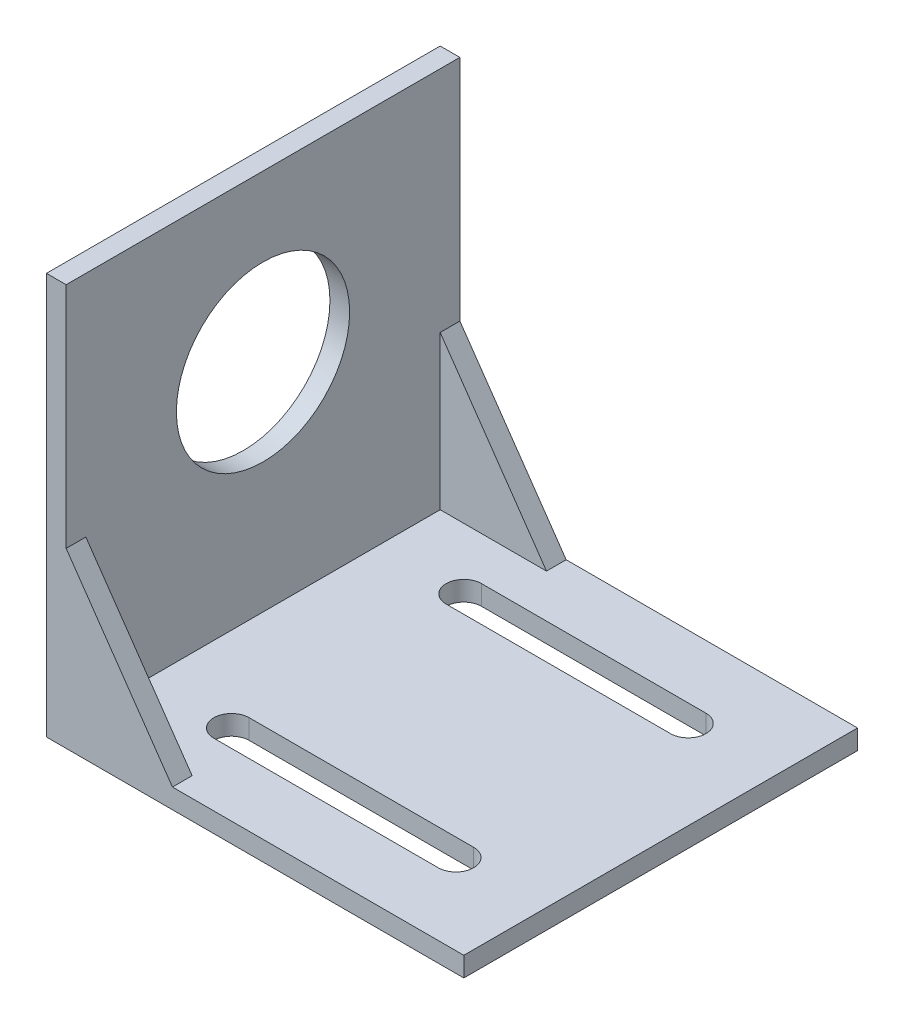
SolidWorks part; units mm, degrees
ref_plane "Front Plane" through (0, 0, 0) normal (0, 0, 1) x (1, 0, 0)
ref_plane "Top Plane" through (0, 0, 0) normal (0, 1, 0) x (1, 0, 0)
ref_plane "Right Plane" through (0, 0, 0) normal (1, 0, 0) x (0, 0, -1)
sketch "Sketch1" plane through (0, 0, 0) normal (0, 0, 1) x (1, 0, 0)
  line L0 (53, 0) -> (0, 0)
  line L1 (0, 0) -> (0, 51)
  line L2 (0, 51) -> (2.5, 51)
  line L3 (2.5, 51) -> (2.5, 2.5)
  line L4 (2.5, 2.5) -> (53, 2.5)
  line L5 (53, 2.5) -> (53, 0)
  dimension "D1" = 51
  dimension "D2" = 53
  dimension "D3" = 2.5
  dimension "D4" = 2.5
extrude "Boss-Extrude1" add sketch "Sketch1" along normal mid plane 50
sketch "Sketch5" plane through (0, 2.5, 0) normal (0, 1, 0) x (1, 0, 0)
  line L0 (13.25, 14.75) -> (41.75, 14.75) construction
  line L1 (13.25, 17) -> (41.75, 17)
  line L2 (13.25, 12.5) -> (41.75, 12.5)
  line L3 (13.25, -14.75) -> (41.75, -14.75) construction
  line L4 (13.25, -12.5) -> (41.75, -12.5)
  line L5 (13.25, -17) -> (41.75, -17)
  line L6 (53, -25) -> (53, 25) construction
  line L7 (0, 0) -> (53, 0) construction
  line L9 (0, -25) -> (0, 25) construction
  line L11 (53, 25) -> (2.5, 25) construction
  line L13 (53, -25) -> (2.5, -25) construction
  arc A0 (13.25, 17) -> (13.25, 12.5) centre (13.25, 14.75) ccw
  arc A1 (41.75, 12.5) -> (41.75, 17) centre (41.75, 14.75) ccw
  arc A2 (13.25, -12.5) -> (13.25, -17) centre (13.25, -14.75) ccw
  arc A3 (41.75, -17) -> (41.75, -12.5) centre (41.75, -14.75) ccw
  point P2 (27.5, 14.75)
  point P7 (27.5, -14.75)
  point P14 (11, -14.75)
  point P18 (44, -14.75)
  point P21 (11, 14.75)
  point P23 (44, 14.75)
  dimension "D1" = 4.5
  dimension "D4" = 11
  dimension "D6" = 33
  dimension "D5" = 9
  dimension "D2" = 4.5
  dimension "D3" = 8
  dimension "D7" = 11
  dimension "D8" = 9
  dimension "D9" = 8
  dimension "D10" = 34
extrude "Cut-Extrude1" cut sketch "Sketch5" against normal blind 10
sketch "Sketch6" plane through (2.5, 0, 0) normal (1, 0, 0) x (0, 0, -1)
  circle A0 centre (0, 30) radius 11
  dimension "D1" = 22
  dimension "D2" = 30
extrude "Cut-Extrude2" cut sketch "Sketch6" against normal blind 10
sketch "Sketch7" plane through (0, 0, 25) normal (0, 0, 1) x (1, 0, 0)
  line L6 (2.5, 2.5) -> (2.5, 51) construction
  line L7 (2.5, 22) -> (16, 2.5)
  line L8 (53, 2.5) -> (2.5, 2.5) construction
  line L9 (16, 2.5) -> (2.5, 2.5)
  line L10 (2.5, 2.5) -> (2.5, 22)
extrude "Boss-Extrude2" add sketch "Sketch7" against normal blind 2.5
mirror "Mirror1" about plane through (0, 0, 0) normal (0, 0, 1) of "Boss-Extrude2"
